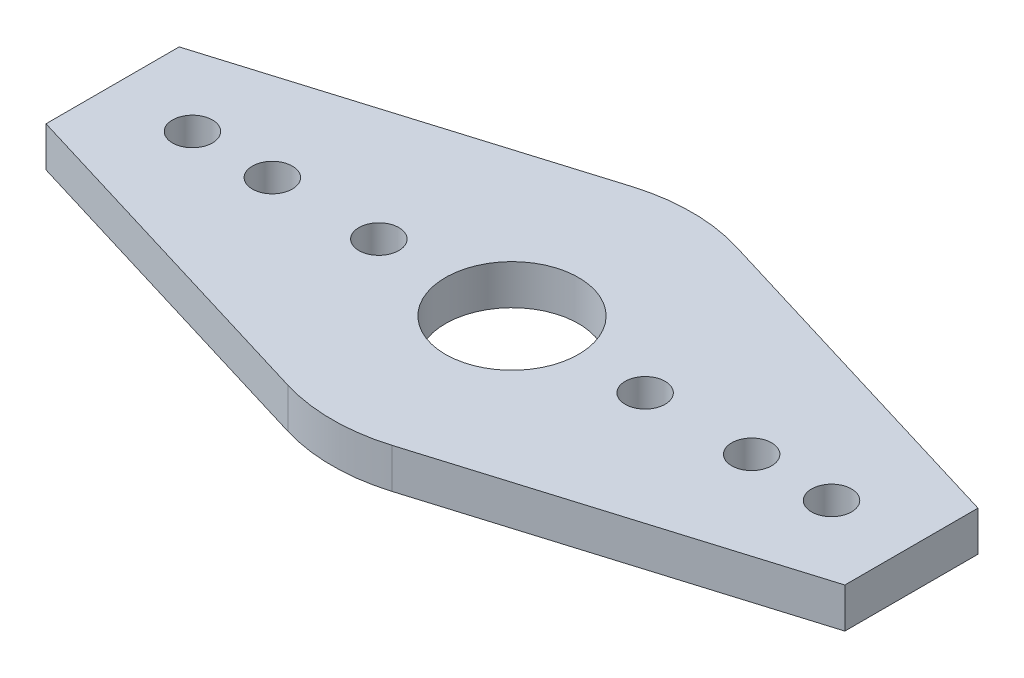
SolidWorks part; units mm, degrees
ref_plane "Front Plane" through (0, 0, 0) normal (0, 0, 1) x (1, 0, 0)
ref_plane "Top Plane" through (0, 0, 0) normal (0, 1, 0) x (1, 0, 0)
ref_plane "Right Plane" through (0, 0, 0) normal (1, 0, 0) x (0, 0, -1)
sketch "Sketch1" plane through (0, 0, 0) normal (0, 1, 0) x (1, 0, 0)
  line L0 (0, 0) -> (0, -27)
  line L1 (30, -13.5) -> (-30, -13.5)
  line L2 (-30, -18.5) -> (-30, -8.5)
  line L3 (-30, -8.5) -> (-3.922, -0.5823)
  line L4 (30, -8.5) -> (3.922, -0.5823)
  line L5 (30, -18.5) -> (30, -8.5)
  line L6 (30, -18.5) -> (3.922, -26.4177)
  line L7 (-30, -18.5) -> (-3.922, -26.4177)
  line L8 (0, -13.5) -> (-10, -13.5)
  line L9 (-30, -13.5) -> (-24, -13.5)
  line L10 (-24, -13.5) -> (-18, -13.5)
  circle A0 centre (0, -13.5) radius 13.5
  circle A1 centre (-10, -13.5) radius 1.5
  circle A2 centre (-24, -13.5) radius 1.5
  circle A3 centre (-18, -13.5) radius 1.5
  circle A4 centre (10, -13.5) radius 1.5
  circle A5 centre (18, -13.5) radius 1.5
  circle A6 centre (24, -13.5) radius 1.5
  circle A7 centre (0, -13.5) radius 5
  dimension "D1" = 5
  dimension "D2" = 13.5
  dimension "D5" = 3
  dimension "D7" = 3
  dimension "D9" = 3
  dimension "D10" = 10
  dimension "D3" = 30
  dimension "D4" = 10
  dimension "D6" = 6
  dimension "D8" = 6
extrude "Boss-Extrude1" add sketch "Sketch1" along normal blind 3 contours A7 L8 A1 L1 A0 L0 | A3 L1 A0 L3 L2 L9 A2 L10 | A3 L10 A2 L9 L2 L7 A0 L1 | A7 L0 A0 L1 A1 L8 | A7 L1 A4 A0 L0 | A7 L0 A0 L1 A4 | L1 A6 A5 A0 L6 L5 | L1 A6 L5 L4 A0 A5
